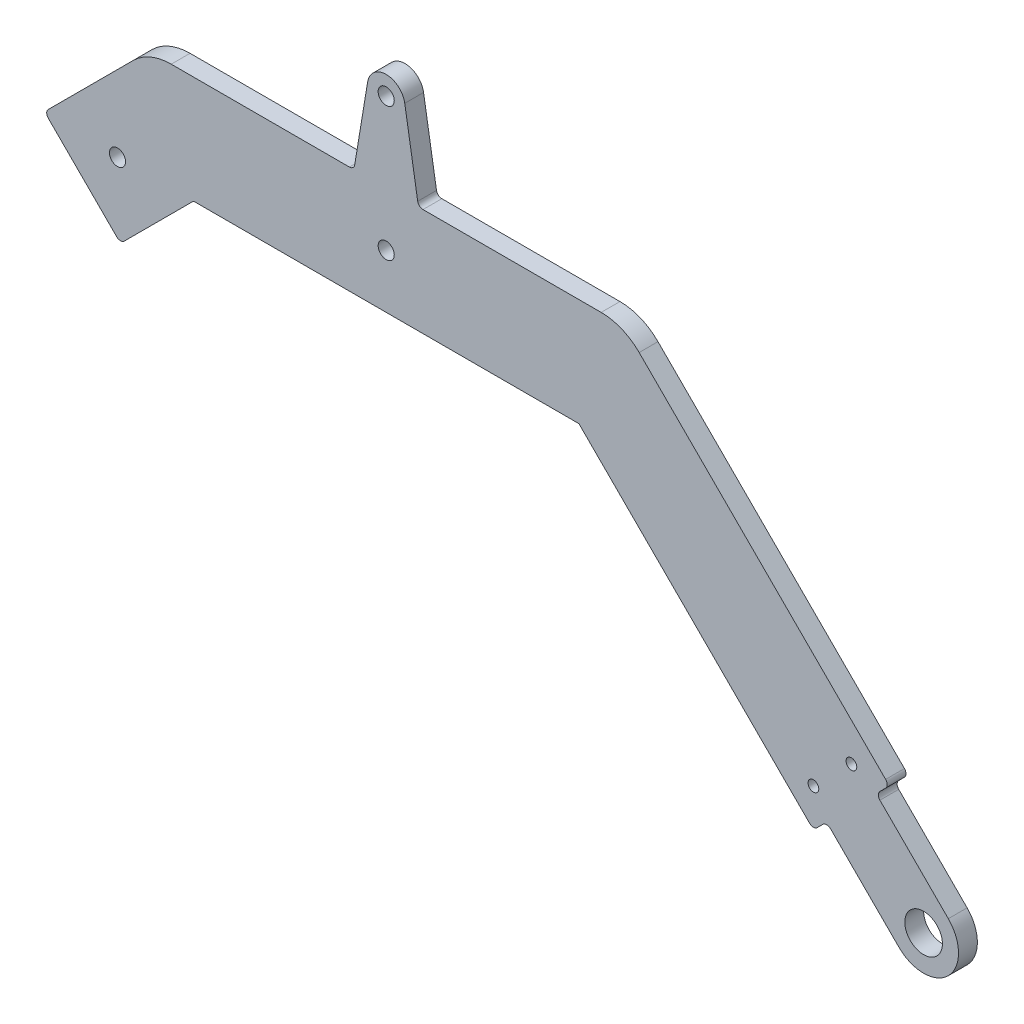
SolidWorks part; units mm, degrees
ref_plane "Front Plane" through (0, 0, 0) normal (0, 0, 1) x (1, 0, 0)
ref_plane "Top Plane" through (0, 0, 0) normal (0, 1, 0) x (1, 0, 0)
ref_plane "Right Plane" through (0, 0, 0) normal (1, 0, 0) x (0, 0, -1)
sketch "Sketch1" plane through (0, 0, 0) normal (0, 0, 1) x (1, 0, 0)
  line L0 (-100, 0) -> (100, 0) construction
  line L1 (0, 0) -> (0, 75.9094) construction
  line L2 (-40, 60) -> (40, 60) construction
  line L4 (0, 99.9354) -> (0, 75.9094) construction
  line L6 (0, 0) -> (-50, 50) construction
  line L7 (-100, 0) -> (0, 100) construction
  line L8 (0, 100) -> (100, 0) construction
  circle A0 centre (-100, 0) radius 20
  circle A1 centre (0, 0) radius 20
  circle A2 centre (100, 0) radius 20
  point P13 (0, 0)
  dimension "D4" = 40
  dimension "D1" = 200
  dimension "D2" = 100
  dimension "D3" = 80
sketch "Sketch3" plane through (0, 0, 0) normal (0, 0, 1) x (1, 0, 0)
  line L0 (-40, 60) -> (-56.5165, 43.4835) construction
  line L1 (81.9688, 8.8388) -> (95.4038, -4.5962)
  line L2 (-40, 60) -> (40, 60) construction
  line L3 (40, 60) -> (86.565, 13.435) construction
  line L4 (0, 100) -> (100, 0) construction
  line L5 (-100, 0) -> (0, 100) construction
  line L6 (44.1421, 70) -> (93.636, 20.5061)
  line L7 (-44.1421, 70) -> (44.1421, 70)
  line L8 (-44.1421, 70) -> (-63.5876, 50.5546)
  line L9 (35.8579, 50) -> (79.4939, 6.364)
  line L10 (-35.8579, 50) -> (35.8579, 50)
  line L11 (-35.8579, 50) -> (-49.4454, 36.4124)
  line L12 (-63.5876, 50.5546) -> (-49.4454, 36.4124)
  line L13 (79.4939, 6.364) -> (93.636, 20.5061)
  line L14 (104.5962, 4.5962) -> (91.1612, 18.0312)
  line L15 (0, 99.9354) -> (0, 75.9094) construction
  line L16 (-3.4532, 85.4203) -> (-6, 70)
  line L17 (3.4532, 85.4203) -> (6, 70)
  line L19 (0, 0) -> (0, 75.9094) construction
  line L20 (75.9584, 9.8995) -> (90.1005, 24.0416) construction
  circle A0 centre (100, 0) radius 10 construction
  circle A1 centre (100, 0) radius 3.5
  arc A2 (95.4038, -4.5962) -> (104.5962, 4.5962) centre (100, 0) ccw
  circle A3 centre (0, 60) radius 1.5
  circle A4 centre (0, 84.85) radius 1.5
  arc A5 (3.4532, 85.4203) -> (-3.4532, 85.4203) centre (0, 84.85) ccw
  circle A6 centre (79.4939, 13.435) radius 1
  circle A7 centre (86.565, 20.5061) radius 1
  circle A8 centre (0, 84.85) radius 3.5 construction
  circle A9 centre (100, 0) radius 6.5 construction
  circle A10 centre (-50, 50) radius 1.5
  point P51 (0, 0)
  point P52 (0, 0)
  dimension "D5" = 20
  dimension "D6" = 7
  dimension "D9" = 3
  dimension "D10" = 3
  dimension "D16" = 2
  dimension "D19" = 3
  dimension "D3" = 27.5
  dimension "D4" = 19
  dimension "D8" = 90
  dimension "D11" = 14.85
  dimension "D12" = 2
  dimension "D13" = 6
  dimension "D14" = 6
  dimension "D15" = 5
  dimension "D17" = 5
  dimension "D18" = 5
  dimension "D1" = 10
  dimension "D2" = 10
  dimension "D7" = 3
sketch "Sketch4" plane through (0, 0, 0) normal (0, 0, 1) x (1, 0, 0)
  line L0 (-86.565, 13.435) -> (-50, 50) construction
  line L1 (-100, 0) -> (0, 100) construction
  line L2 (-50, 50) -> (-13.3744, 13.3744) construction
  line L3 (0, 0) -> (-50, 50) construction
  line L4 (-79.4939, 6.364) -> (-50, 35.8579)
  line L5 (-50, 35.8579) -> (-20.4455, 6.3033)
  line L6 (-93.636, 20.5061) -> (-50, 64.1421)
  line L7 (-50, 64.1421) -> (-6.3033, 20.4455)
  line L8 (-93.636, 20.5061) -> (-79.4939, 6.364)
  line L10 (-82.1491, 9.0191) -> (-95.3424, -4.534)
  line L11 (-91.1612, 18.0312) -> (-104.5962, 4.5962)
  line L12 (-20.4455, 6.3033) -> (-6.3033, 20.4455)
  line L13 (-8.7782, 17.9706) -> (4.5962, 4.5962)
  line L14 (-17.9706, 8.7782) -> (-4.5962, -4.5962)
  line L15 (-90.1005, 24.0416) -> (-75.9584, 9.8995) construction
  line L16 (-23.981, 9.8389) -> (-9.8389, 23.981) construction
  circle A0 centre (-100, 0) radius 10 construction
  circle A1 centre (-100, 0) radius 3.5
  circle A2 centre (0, 0) radius 10 construction
  circle A3 centre (0, 0) radius 3.5
  circle A4 centre (100, 0) radius 10 construction
  arc A5 (-104.5962, 4.5962) -> (-95.3424, -4.534) centre (-100, 0) ccw
  circle A6 centre (100, 0) radius 3.5 construction
  arc A7 (-4.5962, -4.5962) -> (4.5962, 4.5962) centre (0, 0) ccw
  circle A8 centre (-100, 0) radius 20 construction
  circle A9 centre (-50, 50) radius 1.5 construction
  circle A10 centre (0, 0) radius 20 construction
  circle A11 centre (-100, 0) radius 6.5 construction
  circle A12 centre (0, 0) radius 6.5 construction
  circle A13 centre (-86.565, 20.5061) radius 1
  circle A14 centre (-79.4939, 13.435) radius 1
  circle A15 centre (-20.4455, 13.3744) radius 1
  circle A16 centre (-13.3744, 20.4455) radius 1
  circle A17 centre (-50, 50) radius 1.5
  dimension "D7" = 2
  dimension "D4" = 19
  dimension "D5" = 5
  dimension "D6" = 5
  dimension "D8" = 5
  dimension "D9" = 5
  dimension "D10" = 5
  dimension "D11" = 5
  dimension "D1" = 10
  dimension "D2" = 10
  dimension "D3" = 3
sketch "Sketch6" plane through (0, 0, 0) normal (0, 0, 1) x (1, 0, 0)
  line L0 (-57.5, 93.35) -> (57.5, 93.35)
  line L1 (57.5, 93.35) -> (57.5, 83.35)
  line L2 (57.5, 83.35) -> (44.1421, 70)
  line L3 (-57.5, 93.35) -> (-57.5, 83.35)
  line L4 (-57.5, 83.35) -> (-44.1421, 70)
  line L5 (-22.5, 84.85) -> (22.5, 84.85) construction
  line L6 (4, 60) -> (4, 70)
  line L7 (-44.1421, 70) -> (44.1421, 70) construction
  line L8 (-4, 60) -> (-4, 70)
  line L9 (-22.5, 89.35) -> (22.5, 89.35)
  line L12 (-22.5, 80.35) -> (22.5, 80.35)
  circle A0 centre (0, 60) radius 1.5 construction
  circle A1 centre (0, 60) radius 1.5
  arc A2 (-4, 60) -> (4, 60) centre (0, 60) ccw
  arc A5 (-22.5, 89.35) -> (-22.5, 80.35) centre (-22.5, 84.85) ccw
  arc A6 (22.5, 80.35) -> (22.5, 89.35) centre (22.5, 84.85) ccw
  circle A7 centre (0, 60) radius 4 construction
  point P8 (0, 93.35)
  point P23 (0, 84.85)
  point P28 (0, 0)
  dimension "D1" = 115
  dimension "D2" = 10
  dimension "D3" = 2.5
  dimension "D4" = 45
  dimension "D5" = 4
  dimension "D6" = 9
sketch "Sketch7" plane through (0, 0, 0) normal (0, 0, 1) x (1, 0, 0)
  line L0 (81.9688, 8.8388) -> (95.4038, -4.5962) construction
  line L1 (104.5962, 4.5962) -> (91.1612, 18.0312) construction
  line L2 (-3.4532, 85.4203) -> (-6, 70) construction
  line L3 (3.4532, 85.4203) -> (6, 70) construction
  line L4 (81.9688, 8.8388) -> (95.4038, -4.5962)
  line L5 (104.5962, 4.5962) -> (91.1612, 18.0312)
  line L6 (-3.4532, 85.4203) -> (-6, 70)
  line L7 (3.4532, 85.4203) -> (6, 70)
  line L8 (-49.4454, 36.4124) -> (-35.8579, 50)
  line L9 (-63.5876, 50.5546) -> (-49.4454, 36.4124)
  line L10 (-44.1421, 70) -> (-63.5876, 50.5546)
  line L11 (44.1421, 70) -> (-44.1421, 70)
  line L12 (93.636, 20.5061) -> (44.1421, 70)
  line L13 (79.4939, 6.364) -> (93.636, 20.5061)
  line L14 (35.8579, 50) -> (79.4939, 6.364)
  line L15 (-35.8579, 50) -> (35.8579, 50)
  line L16 (-49.4454, 36.4124) -> (-35.8579, 50)
  line L17 (-63.5876, 50.5546) -> (-49.4454, 36.4124)
  line L18 (-44.1421, 70) -> (-63.5876, 50.5546)
  line L19 (44.1421, 70) -> (6, 70)
  line L20 (93.636, 20.5061) -> (44.1421, 70)
  line L21 (79.4939, 6.364) -> (81.9688, 8.8388)
  line L22 (35.8579, 50) -> (79.4939, 6.364)
  line L23 (-35.8579, 50) -> (35.8579, 50)
  line L24 (-6, 70) -> (-44.1421, 70)
  line L25 (91.1612, 18.0312) -> (93.636, 20.5061)
  arc A0 (95.4038, -4.5962) -> (104.5962, 4.5962) centre (100, 0) ccw construction
  circle A1 centre (0, 84.85) radius 1.5
  circle A2 centre (0, 84.85) radius 1.5
  circle A3 centre (0, 60) radius 1.5
  circle A4 centre (0, 60) radius 1.5
  circle A5 centre (100, 0) radius 3.5
  circle A6 centre (100, 0) radius 3.5
  circle A7 centre (86.565, 20.5061) radius 1
  circle A8 centre (86.565, 20.5061) radius 1
  circle A9 centre (79.4939, 13.435) radius 1
  circle A10 centre (79.4939, 13.435) radius 1
  circle A11 centre (-50, 50) radius 1.5
  circle A12 centre (-50, 50) radius 1.5
  arc A13 (3.4532, 85.4203) -> (-3.4532, 85.4203) centre (0, 84.85) ccw construction
  arc A14 (95.4038, -4.5962) -> (104.5962, 4.5962) centre (100, 0) ccw
  arc A15 (3.4532, 85.4203) -> (-3.4532, 85.4203) centre (0, 84.85) ccw
  dimension "D1" = 0
  dimension "D2" = 0
  dimension "D3" = 0
  dimension "D4" = 0
  dimension "D5" = 0
  dimension "D6" = 0
  dimension "D7" = 0
extrude "Boss-Extrude1" add sketch "Sketch7" along normal blind 3.5
fillet "Fillet8" radius 10 2 edges at (-44.1421, 70, 1.75) (44.1421, 70, 1.75)
fillet "Fillet14" radius 1 2 edges at (93.636, 20.5061, 1.75) (91.1612, 18.0312, 1.75)
fillet "Fillet15" radius 1 4 edges at (-63.5876, 50.5546, 1.75) (-49.4454, 36.4124, 1.75) (79.4939, 6.364, 1.75) (81.9688, 8.8388, 1.75)
fillet "Fillet16" radius 1 2 edges at (6, 70, 1.75) (-6, 70, 1.75)
